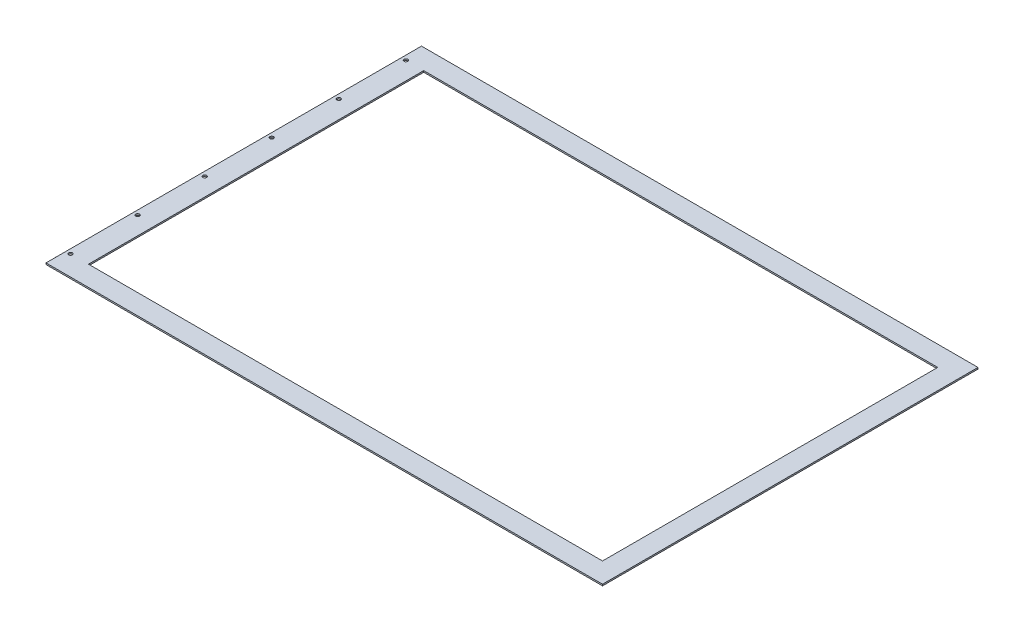
SolidWorks part; units mm, degrees
ref_plane "Front Plane" through (0, 0, 0) normal (0, 0, 1) x (1, 0, 0)
ref_plane "Top Plane" through (0, 0, 0) normal (0, 1, 0) x (1, 0, 0)
ref_plane "Right Plane" through (0, 0, 0) normal (1, 0, 0) x (0, 0, -1)
sketch "Sketch1" plane through (0, 0, 0) normal (0, 1, 0) x (1, 0, 0)
  line L0 (-438.15, 320.04) -> (-438.15, 285.75) construction
  line L1 (-438.15, -285.75) -> (438.15, -285.75)
  line L2 (-438.15, -285.75) -> (-438.15, 285.75)
  line L3 (-438.15, 285.75) -> (438.15, 285.75)
  line L4 (438.15, -285.75) -> (438.15, 285.75)
  line L5 (-438.15, -285.75) -> (438.15, 285.75) construction
  line L6 (-438.15, 285.75) -> (438.15, -285.75) construction
  line L7 (-472.44, -320.04) -> (472.44, -320.04)
  line L8 (-472.44, -320.04) -> (-472.44, 320.04) construction
  line L9 (-472.44, 320.04) -> (472.44, 320.04)
  line L10 (472.44, -320.04) -> (472.44, 320.04)
  line L11 (-472.44, -320.04) -> (472.44, 320.04) construction
  line L12 (-472.44, 320.04) -> (472.44, -320.04) construction
  line L13 (-438.15, 285.75) -> (-472.44, 285.75) construction
  line L14 (-472.44, 320.04) -> (-476.25, 320.04)
  line L15 (-476.25, 320.04) -> (-476.25, -320.04)
  line L16 (-476.25, -320.04) -> (-472.44, -320.04)
  point P0 (0, 0)
  point P6 (0, 0)
  dimension "D1" = 34.29
  dimension "D2" = 571.5
  dimension "D3" = 876.3
  dimension "D4" = 3.81
extrude "Boss-Extrude1" add sketch "Sketch1" along normal blind 2.54
sketch "Sketch2" plane through (0, 2.54, 0) normal (0, 1, 0) x (1, 0, 0)
  line L0 (-468.63, 285.75) -> (-468.63, -285.75)
  line L1 (-468.63, -285.75) -> (-468.63, -320.04) construction
  line L2 (-476.25, -320.04) -> (472.44, -320.04) construction
  line L3 (-468.63, 285.75) -> (-468.63, 320.04) construction
  line L4 (472.44, 320.04) -> (-476.25, 320.04) construction
  line L5 (-476.25, 320.04) -> (-476.25, -320.04) construction
  dimension "D1" = 7.62
  dimension "D2" = 571.5
hole_wizard "1/4 (0.25) Diameter Hole1" positions "3DSketch1" profile "Sketch3" hole size "1/4" standard "ANSI Inch" end condition through all
sketch3d "3DSketch1"
  point P0 (-468.63, 2.54, -285.75)
sketch "Sketch3" plane through (-468.63, 2.54, -285.75) normal (1, 0, 0) x (0, 0, 1)
  line L0 (0, 0) -> (0, 2.54)
  line L1 (0, 2.54) -> (3.175, 2.54)
  line L2 (3.175, 2.54) -> (3.175, 0)
  line L5 (3.175, 0) -> (0, 0)
  line L11 (0, -6.35) -> (0, 107.95) construction
  dimension "Thru Hole Dia." = 6.35
  dimension "Thru Hole Depth" = 2.54
pattern_linear "LPattern1" count 6 spacing 114.3 along (0, 0, 1) of "1/4 (0.25) Diameter Hole1"
